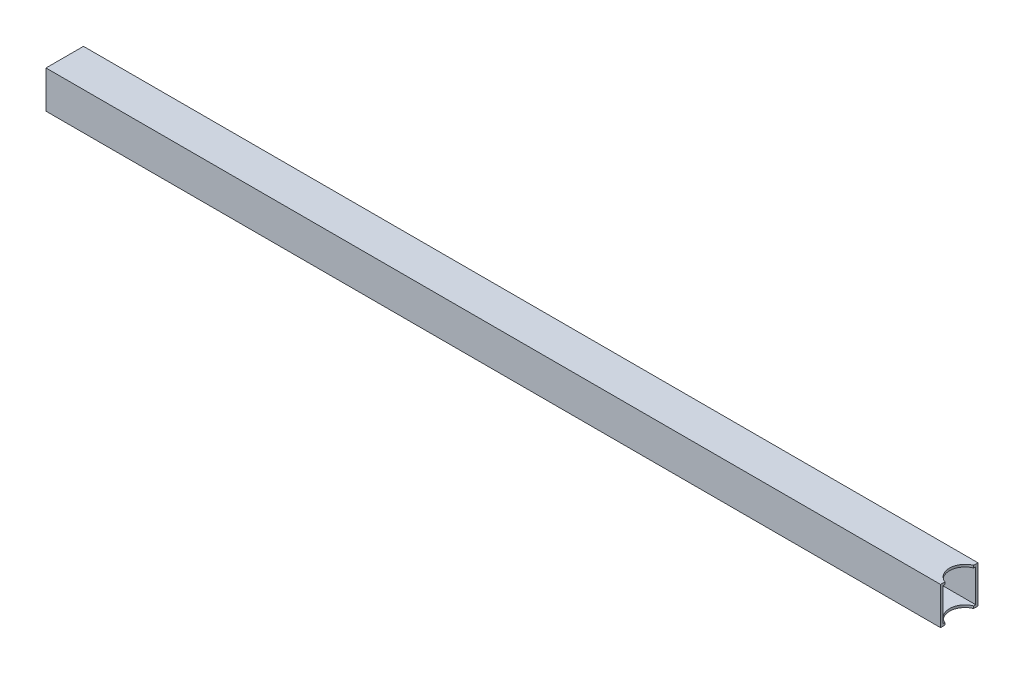
SolidWorks part; units mm, degrees
material "6061-T6 (SS)"
ref_plane "Front Plane" through (0, 0, 0) normal (0, 0, 1) x (1, 0, 0)
ref_plane "Top Plane" through (0, 0, 0) normal (0, 1, 0) x (1, 0, 0)
ref_plane "Right Plane" through (0, 0, 0) normal (1, 0, 0) x (0, 0, -1)
sketch "Sketch1" plane through (0, 0, 0) normal (1, 0, 0) x (0, 0, -1)
  line L1 (-25.4, -25.4) -> (25.4, -25.4)
  line L2 (-25.4, -25.4) -> (-25.4, 25.4)
  line L3 (-25.4, 25.4) -> (25.4, 25.4)
  line L4 (25.4, -25.4) -> (25.4, 25.4)
  line L5 (-25.4, -25.4) -> (25.4, 25.4) construction
  line L6 (-25.4, 25.4) -> (25.4, -25.4) construction
  line L7 (-22.225, -22.225) -> (22.225, -22.225)
  line L8 (-22.225, -22.225) -> (-22.225, 22.225)
  line L9 (-22.225, 22.225) -> (22.225, 22.225)
  line L10 (22.225, -22.225) -> (22.225, 22.225)
  line L11 (-22.225, -22.225) -> (22.225, 22.225) construction
  line L12 (-22.225, 22.225) -> (22.225, -22.225) construction
  point P0 (0, 0)
  point P6 (0, 0)
  dimension "D1" = 50.8
  dimension "D2" = 3.175
  dimension "D3" = 50.8
extrude "Boss-Extrude1" add sketch "Sketch1" along normal blind 590.55 and the other way blind 590.55
sketch "Sketch6" plane through (590.55, 0, 0) normal (1, 0, 0) x (0, 0, -1)
  line L0 (-22.225, -22.225) -> (22.225, -22.225) construction
  line L1 (22.225, -22.225) -> (22.225, 22.225) construction
  line L2 (22.225, 22.225) -> (-22.225, 22.225) construction
  line L3 (-22.225, 22.225) -> (-22.225, -22.225) construction
  line L4 (25.4, -25.4) -> (25.4, 25.4)
  line L5 (25.4, 25.4) -> (-25.4, 25.4)
  line L6 (-25.4, 25.4) -> (-25.4, -25.4)
  line L7 (-25.4, -25.4) -> (25.4, -25.4)
  line L8 (25.4, -25.4) -> (25.4, 25.4)
  line L9 (25.4, 25.4) -> (-25.4, 25.4)
  line L10 (-25.4, 25.4) -> (-25.4, -25.4)
  line L11 (-25.4, -25.4) -> (25.4, -25.4)
  line L12 (-22.225, -22.225) -> (22.225, -22.225)
  line L13 (22.225, -22.225) -> (22.225, 22.225)
  line L14 (22.225, 22.225) -> (-22.225, 22.225)
  line L15 (-22.225, 22.225) -> (-22.225, -22.225)
  dimension "D1" = 0
extrude "Boss-Extrude2" add sketch "Sketch6" along normal blind 31.75
sketch "Sketch7" plane through (0, 25.4, 0) normal (0, 1, 0) x (1, 0, 0)
  line L0 (584.2, 25.4) -> (584.2, -25.4) construction
  line L1 (-590.55, 25.4) -> (622.3, 25.4) construction
  line L2 (-590.55, -25.4) -> (622.3, -25.4) construction
  line L3 (622.3, 25.4) -> (622.3, -25.4) construction
  circle A0 centre (630.2375, 0) radius 21.082
  dimension "D3" = 42.164
  dimension "D1" = 38.1
  dimension "D2" = 46.0375
  dimension "D4" = 25.4
extrude "Cut-Extrude1" cut sketch "Sketch7" against normal blind 50.8
